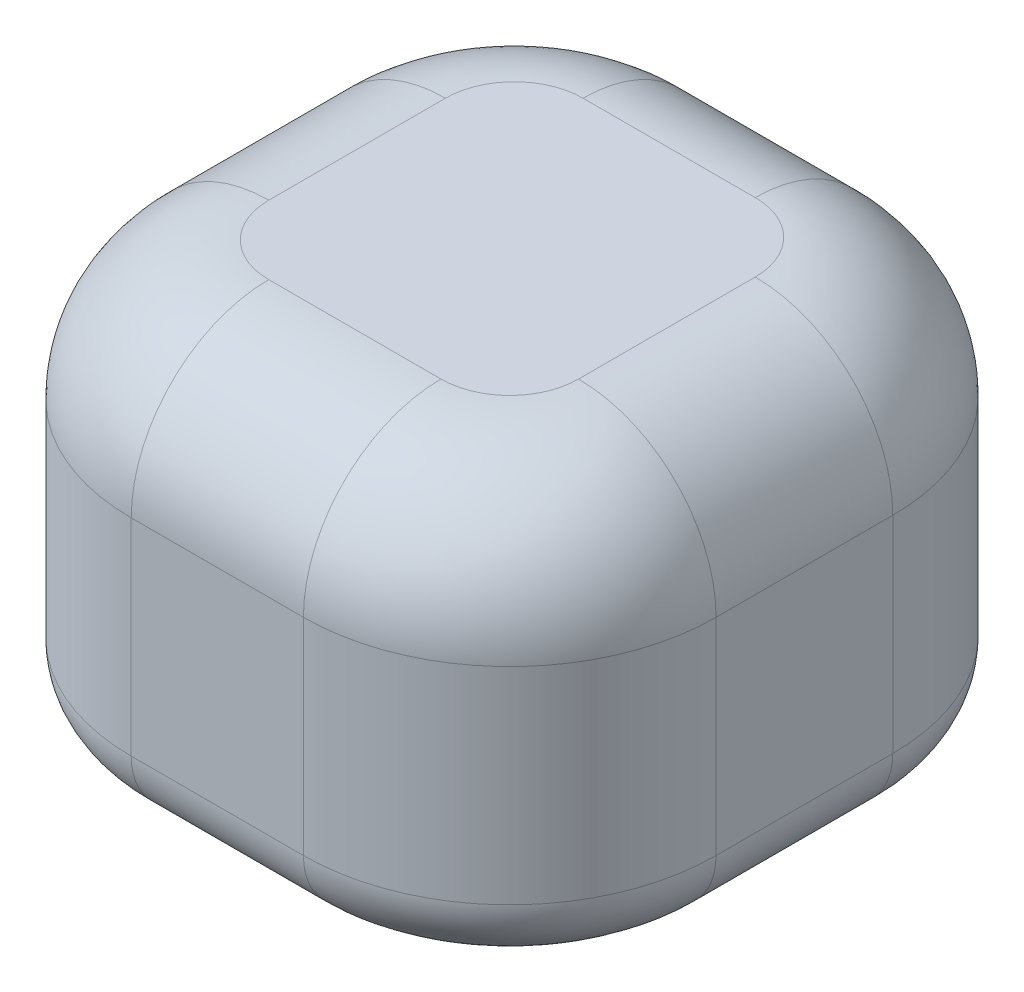
SolidWorks part; units mm, degrees
ref_plane "Front Plane" through (0, 0, 0) normal (0, 0, 1) x (1, 0, 0)
ref_plane "Top Plane" through (0, 0, 0) normal (0, 1, 0) x (1, 0, 0)
ref_plane "Right Plane" through (0, 0, 0) normal (1, 0, 0) x (0, 0, -1)
sketch "Sketch1" plane through (0, 0, 0) normal (0, 1, 0) x (1, 0, 0)
  line L0 (-94.993, -80.5265) -> (108.0769, 65.2905) construction
  line L1 (-42.52, -42.8476) -> (42.52, -42.8476)
  line L2 (-42.52, -42.8476) -> (-42.52, 42.8476)
  line L3 (-42.52, 42.8476) -> (42.52, 42.8476)
  line L4 (42.52, -42.8476) -> (42.52, 42.8476)
  line L5 (-42.52, -42.8476) -> (42.52, 42.8476) construction
  line L6 (-42.52, 42.8476) -> (42.52, -42.8476) construction
  point P0 (0, 0)
extrude "Boss-Extrude1" add sketch "Sketch1" along normal blind 30 and the other way blind 30
fillet "Fillet1" radius 30 4 edges at (42.52, 0, 42.8476) (42.52, 0, -42.8476) (-42.52, 0, 42.8476) (-42.52, 0, -42.8476)
fillet "Fillet2" radius 20 8 edges at (-33.7332, 30, 34.0608) (-42.52, 30, 0) (-33.7332, 30, -34.0608) (0, 30, -42.8476) (33.7332, 30, -34.0608) (42.52, 30, 0) (33.7332, 30, 34.0608) (0, 30, 42.8476)
fillet "Fillet3" radius 10 8 edges at (33.7332, -30, -34.0608) (0, -30, -42.8476) (-33.7332, -30, -34.0608) (-42.52, -30, 0) (-33.7332, -30, 34.0608) (0, -30, 42.8476) (33.7332, -30, 34.0608) (42.52, -30, 0)
